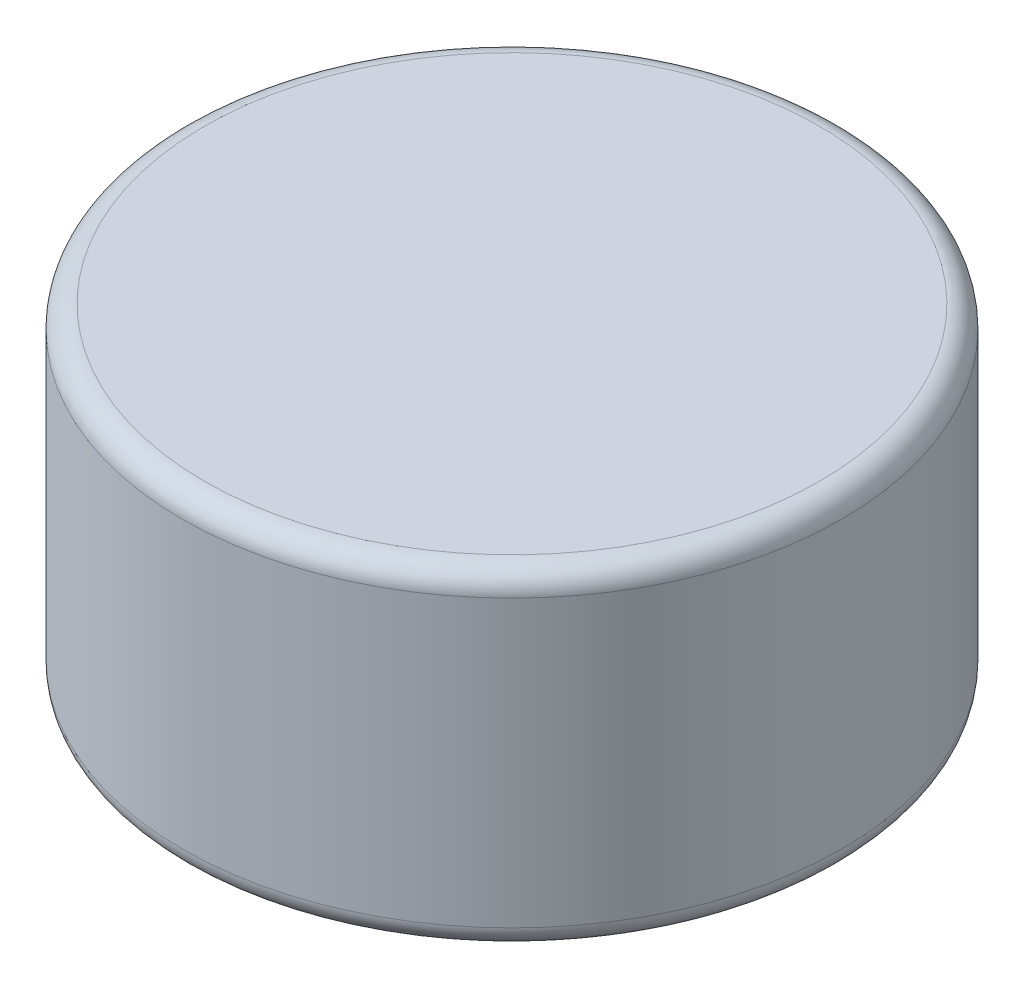
SolidWorks part; units mm, degrees
material "1023 Carbon Steel Sheet (SS)"
ref_plane "Front Plane" through (0, 0, 0) normal (0, 0, 1) x (1, 0, 0)
ref_plane "Top Plane" through (0, 0, 0) normal (0, 1, 0) x (1, 0, 0)
ref_plane "Right Plane" through (0, 0, 0) normal (1, 0, 0) x (0, 0, -1)
sketch "Sketch1" plane through (0, 0, 0) normal (0, 1, 0) x (1, 0, 0)
  circle A0 centre (0, 0) radius 3
  dimension "D1" = 6
extrude "Boss-Extrude1" add sketch "Sketch1" along normal mid plane 3
fillet "Fillet1" radius 0.2 2 edges at (0, -1.5, 3) (0, 1.5, 3)
